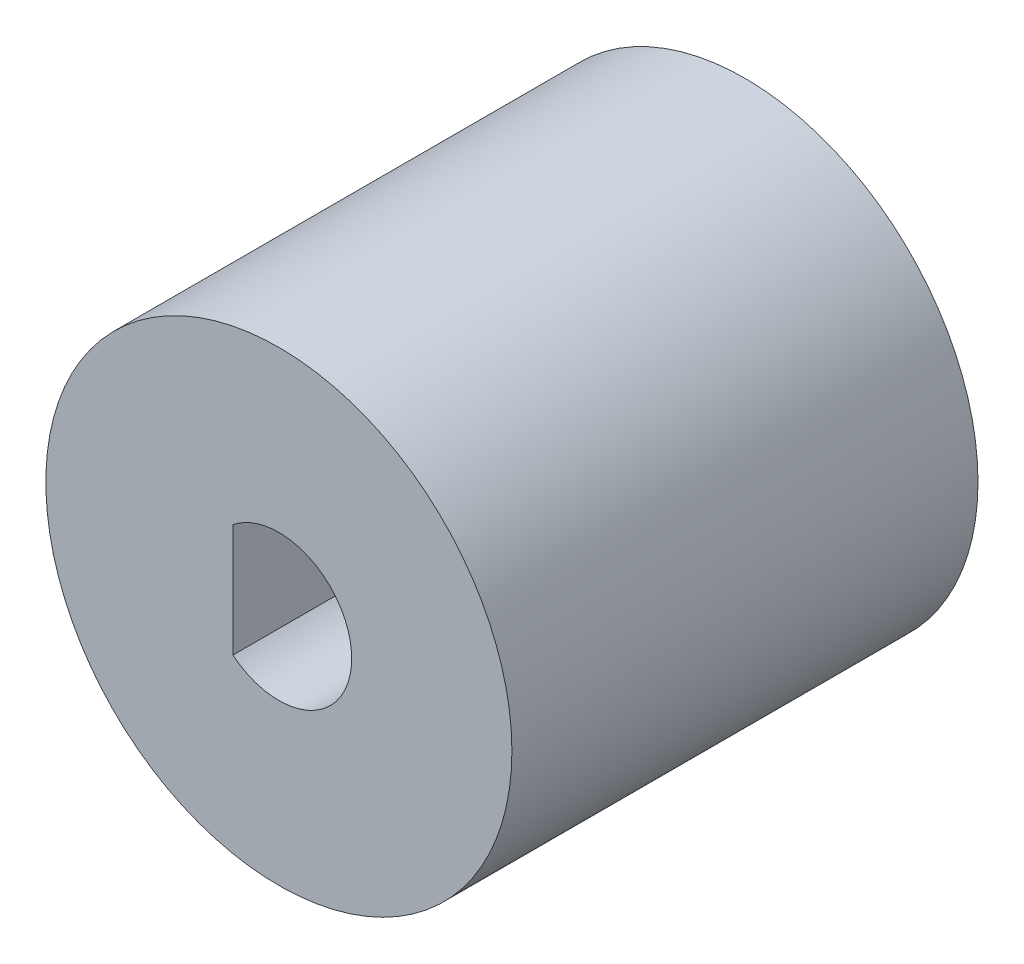
SolidWorks part; units mm, degrees
ref_plane "前视基准面" through (0, 0, 0) normal (0, 0, 1) x (1, 0, 0)
ref_plane "上视基准面" through (0, 0, 0) normal (0, 1, 0) x (1, 0, 0)
ref_plane "右视基准面" through (0, 0, 0) normal (1, 0, 0) x (0, 0, -1)
sketch "草图1" plane through (0, 0, 0) normal (0, 0, 1) x (1, 0, 0)
  circle A0 centre (0, 0) radius 8
extrude "凸台-拉伸1" add sketch "草图1" along normal blind 16
sketch "草图2" plane through (0, 0, 0) normal (0, 0, -1) x (-1, 0, 0)
  line L0 (3.0206, 2.6223) -> (3.0206, -2.6223)
  arc A3 (3.0206, -2.6223) -> (3.0206, 2.6223) centre (0, 0) cw
extrude "切除-拉伸1" cut sketch "草图2" against normal blind 8
sketch "草图3" plane through (0, 0, 16) normal (0, 0, 1) x (1, 0, 0)
  line L0 (-1.5789, -1.9383) -> (-1.5789, 1.9383)
  arc A1 (-1.5789, 1.9383) -> (-1.5789, -1.9383) centre (0, 0) cw
extrude "切除-拉伸2" cut sketch "草图3" against normal blind 8
